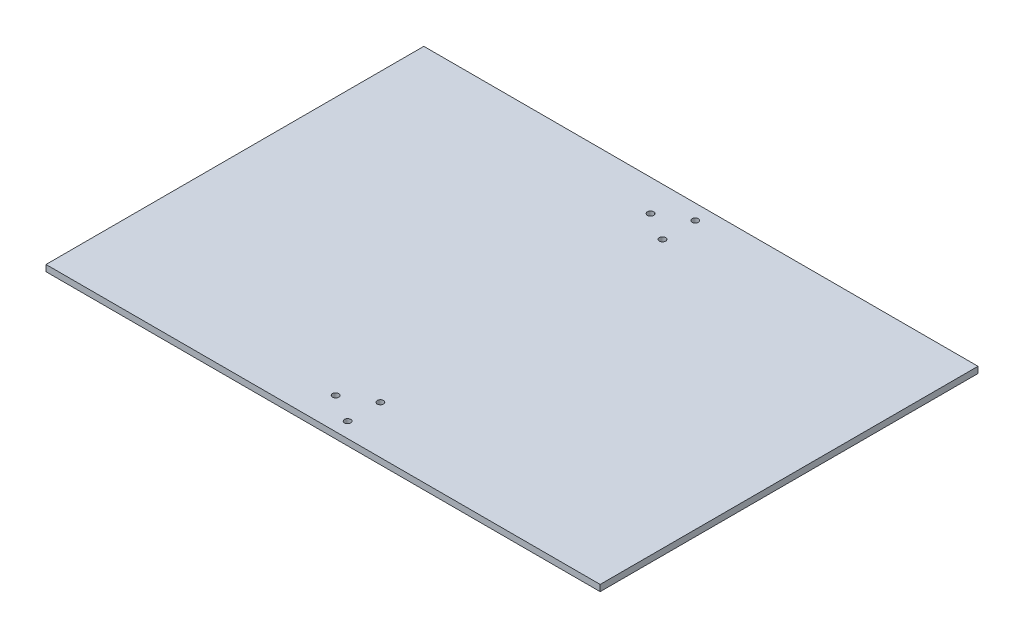
SolidWorks part; units mm, degrees
ref_plane "Front Plane" through (0, 0, 0) normal (0, 0, 1) x (1, 0, 0)
ref_plane "Top Plane" through (0, 0, 0) normal (0, 1, 0) x (1, 0, 0)
ref_plane "Right Plane" through (0, 0, 0) normal (1, 0, 0) x (0, 0, -1)
sketch "Sketch1" plane through (0, 0, 0) normal (0, 1, 0) x (1, 0, 0)
  line L0 (0, -317.5) -> (0, 317.5)
  line L1 (-558.8, 381) -> (558.8, 381)
  line L2 (-558.8, 381) -> (-558.8, -381)
  line L3 (-558.8, -381) -> (558.8, -381)
  line L4 (558.8, 381) -> (558.8, -381)
  line L5 (-558.8, 381) -> (558.8, -381) construction
  line L6 (-558.8, -381) -> (558.8, 381) construction
  line L7 (-236.0518, 0) -> (266.1708, 0) construction
  circle A0 centre (0, 317.5) radius 50.8
  circle A1 centre (0, -317.5) radius 50.8
  circle A2 centre (-35.56, 317.5) radius 6.35
  circle A4 centre (17.78, 348.2959) radius 6.35
  circle A5 centre (17.78, 286.7041) radius 6.35
  circle A6 centre (17.78, -286.7041) radius 6.35
  circle A7 centre (17.78, -348.2959) radius 6.35
  circle A8 centre (-35.56, -317.5) radius 6.35
  point P0 (0, 0)
  point P11 (0, 0)
  point P15 (0, 0)
  point P26 (0, 0)
  dimension "D4" = 101.6
  dimension "D5" = 101.6
  dimension "D7" = 12.7
  dimension "D9" = 12.7
  dimension "D10" = 12.7
  dimension "D1" = 762
  dimension "D2" = 1117.6
  dimension "D3" = 635
  dimension "D6" = 35.56
extrude "Boss-Extrude3" add sketch "Sketch1" against normal blind 12.7
sketch "Sketch3" plane through (0, 0, 0) normal (0, 1, 0) x (1, 0, 0)
  line L0 (0, -317.5) -> (0, 317.5) construction
  line L1 (-170.1151, 0) -> (226.8201, 0) construction
  line L2 (0, 317.5) -> (-38.1, 317.5) construction
  line L3 (0, 317.5) -> (19.05, 350.4956) construction
  line L4 (0, 317.5) -> (19.05, 284.5044) construction
  circle A0 centre (0, 317.5) radius 50.8
  circle A2 centre (-38.1, 317.5) radius 6.35
  circle A3 centre (19.05, 350.4956) radius 6.35
  circle A4 centre (19.05, 284.5044) radius 6.35
  circle A5 centre (19.05, -350.4956) radius 6.35
  circle A6 centre (19.05, -284.5044) radius 6.35
  circle A7 centre (-38.1, -317.5) radius 6.35
  circle A8 centre (0, -317.5) radius 50.8
  point P6 (0, 0)
  dimension "D2" = 101.6
  dimension "D6" = 12.7
  dimension "D7" = 12.7
  dimension "D8" = 12.7
  dimension "D1" = 635
  dimension "D4" = 120
  dimension "D5" = 120
extrude "Cut-Extrude1" cut sketch "Sketch3" against normal blind 12.7 contours A4 | A2 | A3 | A5 | A7 | A6
